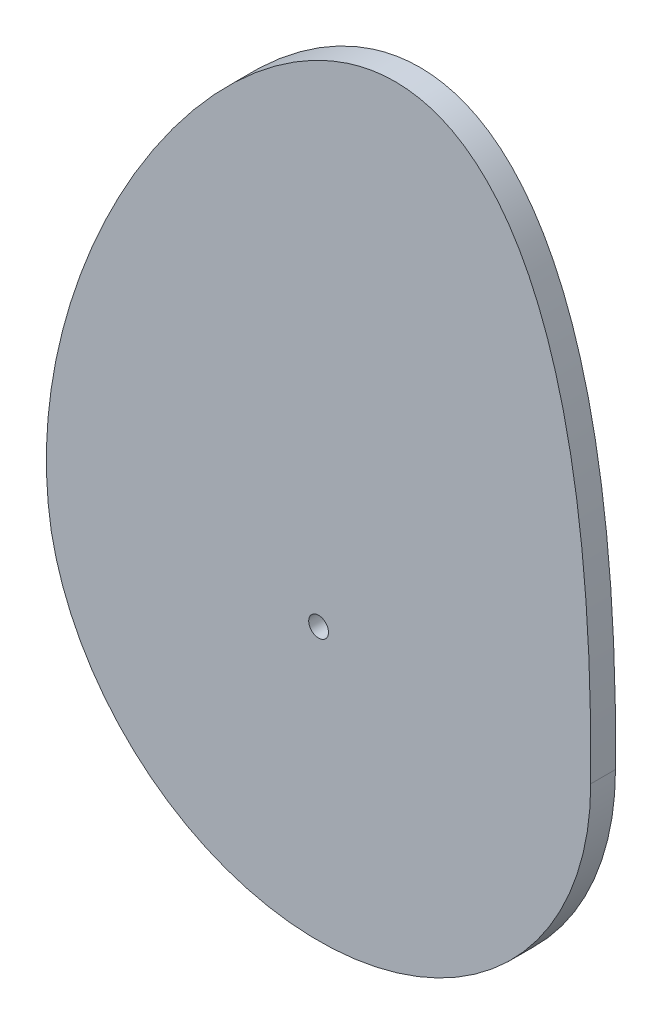
SolidWorks part; units mm, degrees
ref_plane "Front Plane" through (0, 0, 0) normal (0, 0, 1) x (1, 0, 0)
ref_plane "Top Plane" through (0, 0, 0) normal (0, 1, 0) x (1, 0, 0)
ref_plane "Right Plane" through (0, 0, 0) normal (1, 0, 0) x (0, 0, -1)
sketch "Sketch1" plane through (0, 0, 0) normal (0, 0, 1) x (1, 0, 0)
  circle A0 centre (0, 0) radius 55
  circle A1 centre (0, 0) radius 2
  spline S0 degree 3 poles (55, 0) (56.7619, 195.8578) (-67.1736, 66.3981) (-54.0443, -10.2084) knots 0 0 0 0 1 1 1 1
  point P7 (0, 99.1407)
  dimension "D1" = 4
  dimension "D2" = 110
extrude "Boss-Extrude1" add sketch "Sketch1" along normal blind 5 contours A0 S0 | A0 S0
